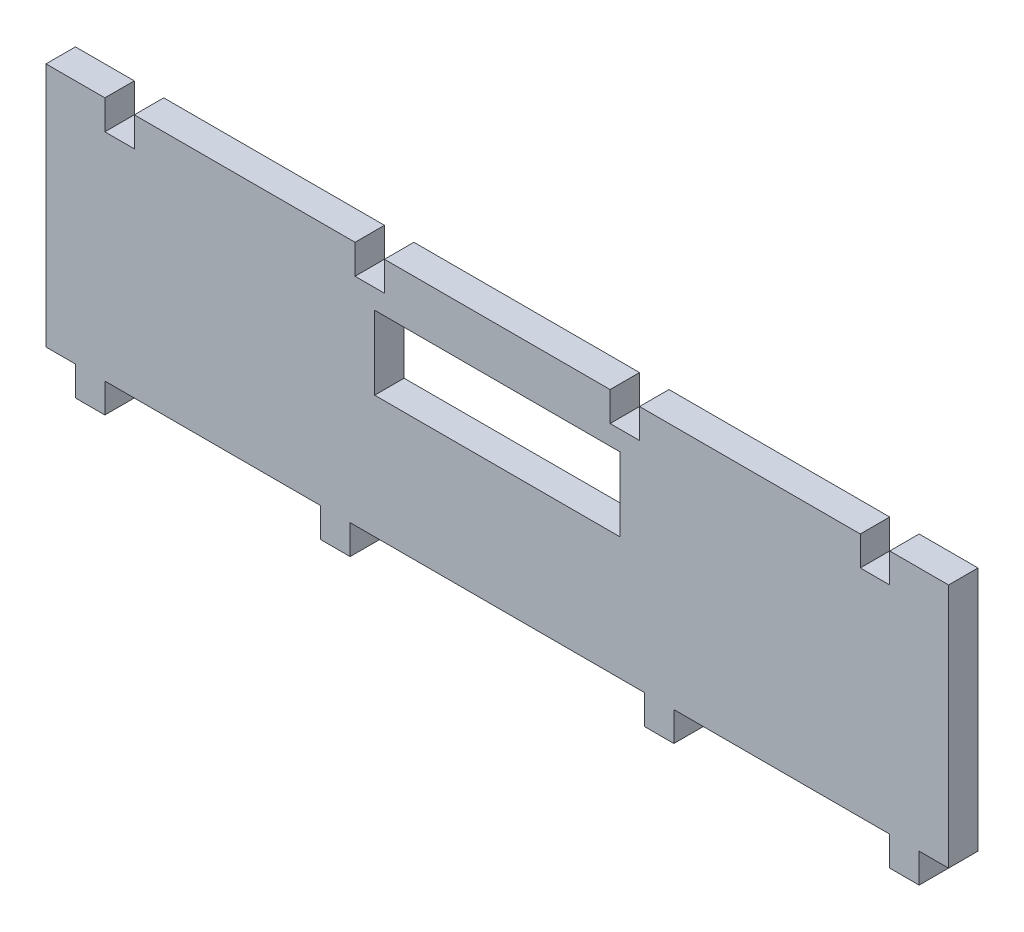
SolidWorks part; units mm, degrees
material "Pine"
ref_plane "정면" through (0, 0, 0) normal (0, 0, 1) x (1, 0, 0)
ref_plane "윗면" through (0, 0, 0) normal (0, 1, 0) x (1, 0, 0)
ref_plane "우측면" through (0, 0, 0) normal (1, 0, 0) x (0, 0, -1)
sketch "Sketch1" plane through (0, 0, 0) normal (0, 0, 1) x (1, 0, 0)
  line L0 (0, -70.5085) -> (0, 94.3844) construction
  line L5 (92, 0) -> (-92, 0)
  line L6 (-92, 0) -> (-92, 50)
  line L7 (-92, 50) -> (92, 50)
  line L8 (92, 0) -> (92, 50)
  point P8 (0, 0)
  point P9 (0, 50)
  dimension "D1" = 92
  dimension "D2" = 50
extrude "Boss-Extrude2" add sketch "Sketch1" along normal blind 6
sketch "Sketch5" plane through (0, 0, 6) normal (0, 0, 1) x (1, 0, 0)
  line L0 (0, -47.1058) -> (0, 141.238) construction
  line L1 (-86, 0) -> (-86, -6)
  line L2 (-92, 0) -> (92, 0) construction
  line L3 (-86, -6) -> (-80, -6)
  line L4 (-80, -6) -> (-80, 0)
  line L5 (-80, 0) -> (-86, 0)
  line L6 (-92, 50) -> (-92, 0) construction
  line L7 (-36, 0) -> (-36, -6)
  line L8 (-36, -6) -> (-30, -6)
  line L9 (-30, -6) -> (-30, 0)
  line L10 (-30, 0) -> (-36, 0)
  line L11 (30, 0) -> (36, 0)
  line L12 (30, -6) -> (30, 0)
  line L13 (36, -6) -> (30, -6)
  line L14 (36, 0) -> (36, -6)
  line L15 (80, 0) -> (86, 0)
  line L16 (80, -6) -> (80, 0)
  line L17 (86, -6) -> (80, -6)
  line L18 (86, 0) -> (86, -6)
  dimension "D1" = 6
  dimension "D2" = 6
  dimension "D3" = 6
  dimension "D4" = 6
  dimension "D5" = 6
  dimension "D6" = 30
sketch "Sketch7" plane through (0, 0, 0) normal (0, 0, 1) x (1, 0, 0)
  line L0 (0, -47.9339) -> (0, 131.0274) construction
  line L1 (92, 50) -> (-92, 50) construction
  line L2 (74, 50) -> (74, 44)
  line L3 (74, 44) -> (80, 44)
  line L4 (80, 44) -> (80, 50)
  line L5 (80, 50) -> (74, 50)
  line L6 (92, 0) -> (92, 50) construction
  line L7 (23, 50) -> (23, 44)
  line L8 (23, 44) -> (29, 44)
  line L9 (29, 44) -> (29, 50)
  line L10 (29, 50) -> (23, 50)
  line L11 (92, 50) -> (-92, 50) construction
  line L12 (-80, 50) -> (-74, 50)
  line L13 (-80, 44) -> (-80, 50)
  line L14 (-74, 44) -> (-80, 44)
  line L15 (-74, 50) -> (-74, 44)
  line L16 (-29, 50) -> (-23, 50)
  line L17 (-29, 44) -> (-29, 50)
  line L18 (-23, 44) -> (-29, 44)
  line L19 (-23, 50) -> (-23, 44)
  dimension "D1" = 6
  dimension "D2" = 6
  dimension "D3" = 12
  dimension "D4" = 6
  dimension "D5" = 6
  dimension "D6" = 45
extrude "Cut-Extrude3" cut sketch "Sketch7" along normal blind 6
sketch "Sketch8" plane through (0, 0, 0) normal (0, 0, -1) x (-1, 0, 0)
  line L0 (0, -37.6281) -> (0, 96.5585) construction
  line L1 (-25, 25) -> (25, 25)
  line L2 (25, 25) -> (25, 40)
  line L3 (25, 40) -> (-25, 40)
  line L4 (92, 0) -> (-92, 0) construction
  line L5 (-25, 25) -> (-25, 40)
  point P10 (0, 40)
  point P11 (0, 25)
  dimension "D1" = 25
  dimension "D2" = 15
  dimension "D3" = 25
extrude "Cut-Extrude4" cut sketch "Sketch8" against normal blind 6
sketch "Sketch9" plane through (0, 0, 0) normal (0, -1, 0) x (1, 0, 0)
  line L0 (0, -53.4889) -> (0, 70.5125) construction
  line L1 (-86, 6) -> (-86, 0)
  line L2 (-86, 0) -> (-80, 0)
  line L3 (-80, 0) -> (-80, 6)
  line L4 (-80, 6) -> (-86, 6)
  line L5 (-36, 6) -> (-36, 0)
  line L6 (-36, 0) -> (-30, 0)
  line L7 (-30, 0) -> (-30, 6)
  line L8 (-30, 6) -> (-36, 6)
  line L9 (-92, 6) -> (92, 6) construction
  line L10 (-92, 6) -> (-92, 0) construction
  line L11 (30, 6) -> (36, 6)
  line L12 (30, 0) -> (30, 6)
  line L13 (36, 0) -> (30, 0)
  line L14 (36, 6) -> (36, 0)
  line L15 (80, 6) -> (86, 6)
  line L16 (80, 0) -> (80, 6)
  line L17 (86, 0) -> (80, 0)
  line L18 (86, 6) -> (86, 0)
  dimension "D1" = 6
  dimension "D2" = 6
  dimension "D3" = 6
  dimension "D4" = 6
  dimension "D5" = 6
  dimension "D6" = 30
extrude "Boss-Extrude3" add sketch "Sketch9" along normal blind 6
